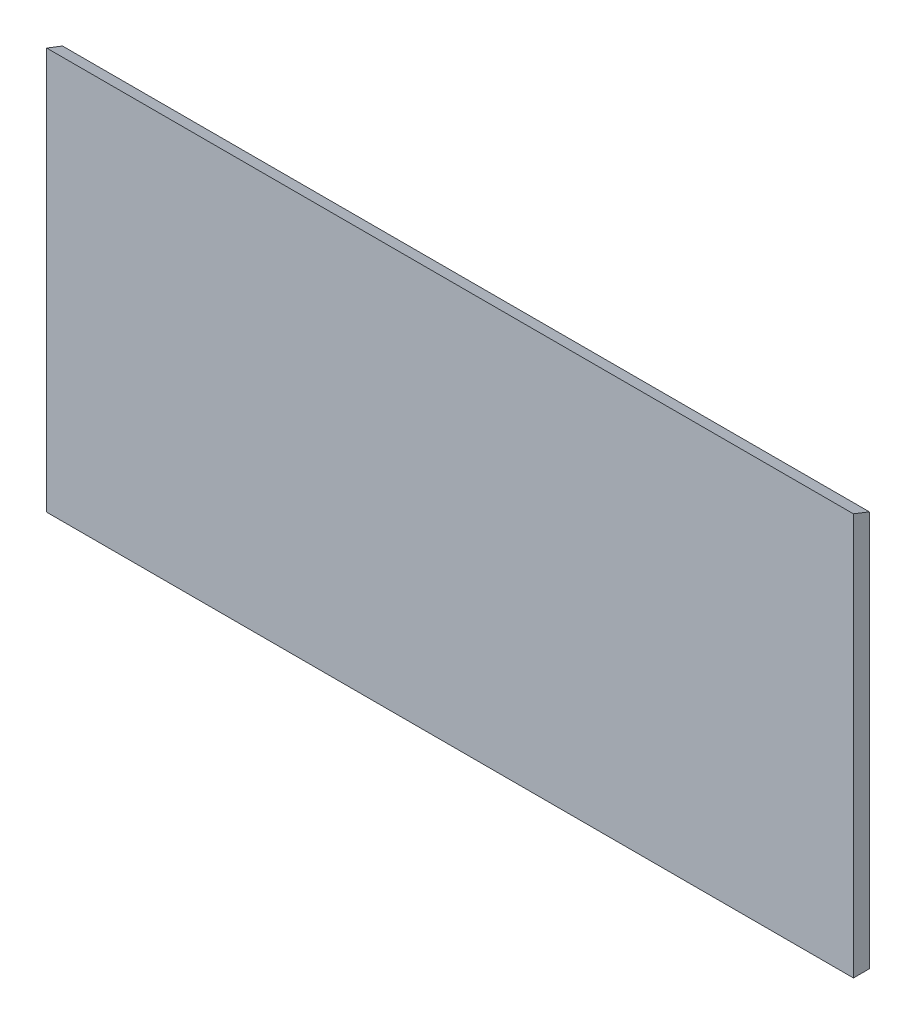
SolidWorks part; units mm, degrees
ref_plane "Front" through (0, 0, 0) normal (0, 0, 1) x (1, 0, 0)
ref_plane "Top" through (0, 0, 0) normal (0, 1, 0) x (1, 0, 0)
ref_plane "Right" through (0, 0, 0) normal (1, 0, 0) x (0, 0, -1)
sketch "Sketch1" plane through (0, 0, 0) normal (0, 0, 1) x (1, 0, 0)
  line L1 (850, 417) -> (-850, 417)
  line L2 (850, 417) -> (850, -417)
  line L3 (850, -417) -> (-850, -417)
  line L4 (-850, 417) -> (-850, -417)
  line L5 (850, 417) -> (-850, -417) construction
  line L6 (850, -417) -> (-850, 417) construction
  point P1 (0, 0)
  dimension "D1" = 1700
  dimension "D2" = 834
extrude "Boss-Extrude1" add sketch "Sketch1" along normal blind 33.45
sketch "Sketch2" plane through (850, 0, 0) normal (1, 0, 0) x (0, 0, -1)
  line L0 (-33.45, 417) -> (-33.45, 430)
  line L1 (-33.45, 430) -> (0, 417)
  line L2 (0, 417) -> (-33.45, 417)
  dimension "D1" = 13
extrude "Boss-Extrude2" add sketch "Sketch2" against normal up to surface (1700 mm away) up to face at (-850, 0, 16.725)
